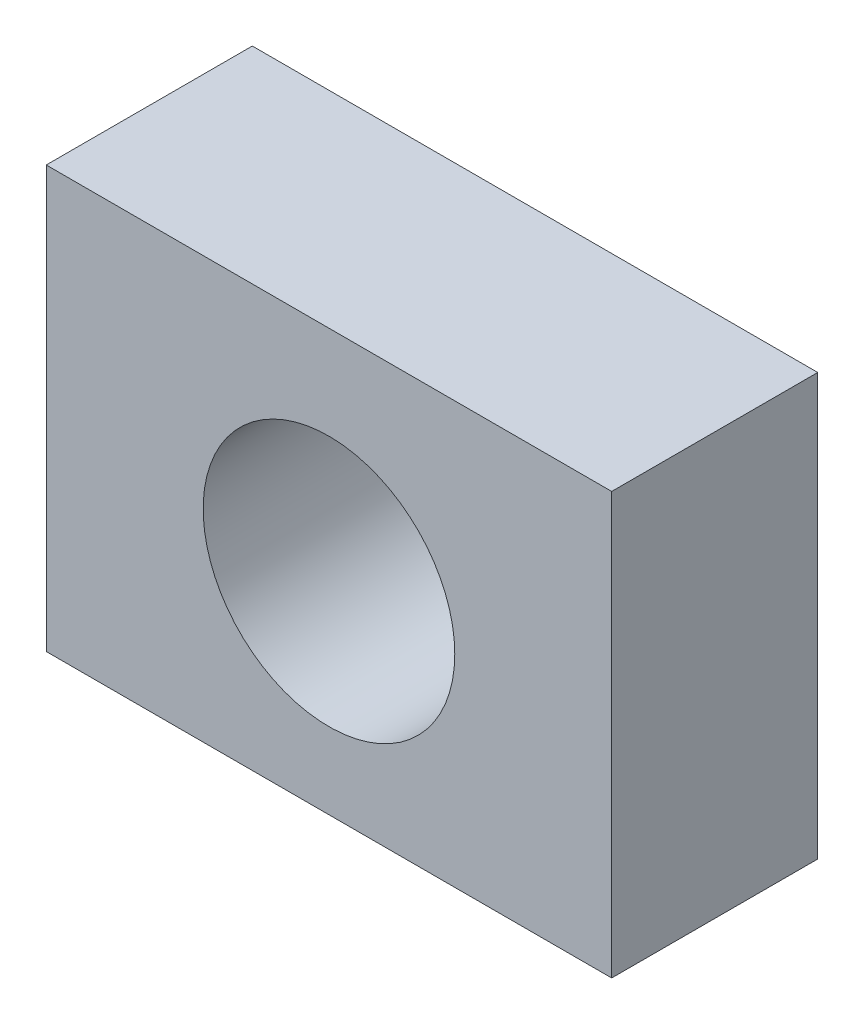
SolidWorks part; units mm, degrees
ref_plane "Front Plane" through (0, 0, 0) normal (0, 0, 1) x (1, 0, 0)
ref_plane "Top Plane" through (0, 0, 0) normal (0, 1, 0) x (1, 0, 0)
ref_plane "Right Plane" through (0, 0, 0) normal (1, 0, 0) x (0, 0, -1)
sketch "Sketch1" plane through (0, 0, 0) normal (0, 0, 1) x (1, 0, 0)
  line L1 (-31.1704, 26.6057) -> (37.4306, 26.6057)
  line L2 (-31.1704, 26.6057) -> (-31.1704, -24.519)
  line L3 (-31.1704, -24.519) -> (37.4306, -24.519)
  line L4 (37.4306, 26.6057) -> (37.4306, -24.519)
  circle A0 centre (3.1301, 0) radius 15.2636
extrude "Boss-Extrude1" add sketch "Sketch1" along normal blind 25
